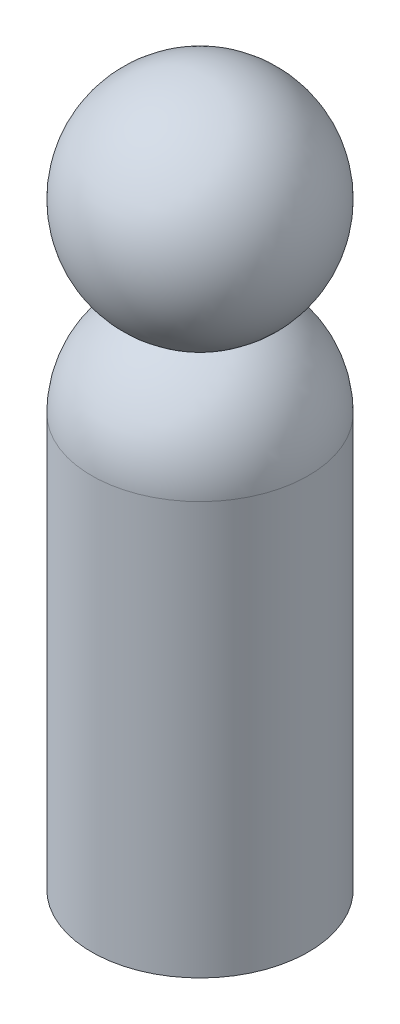
SolidWorks part; units mm, degrees
ref_plane "Front Plane" through (0, 0, 0) normal (0, 0, 1) x (1, 0, 0)
ref_plane "Top Plane" through (0, 0, 0) normal (0, 1, 0) x (1, 0, 0)
ref_plane "Right Plane" through (0, 0, 0) normal (1, 0, 0) x (0, 0, -1)
sketch "Sketch1" plane through (0, 0, 0) normal (0, 0, 1) x (1, 0, 0)
  line L0 (0, 0) -> (0, 139.7)
  line L1 (0, 0) -> (21.4312, 0)
  line L2 (21.4312, 0) -> (21.4312, 81.6026)
  arc A0 (0, 96.8375) -> (0, 139.7) centre (0, 118.2687) ccw
  arc A1 (21.4312, 81.6026) -> (10.5347, 99.6054) centre (1.1113, 81.6026) ccw
  dimension "D2" = 42.8625
  dimension "D4" = 20.32
  dimension "D1" = 139.7
  dimension "D3" = 21.4312
revolve "Revolve1" add sketch "Sketch1" angle 360 about L0
